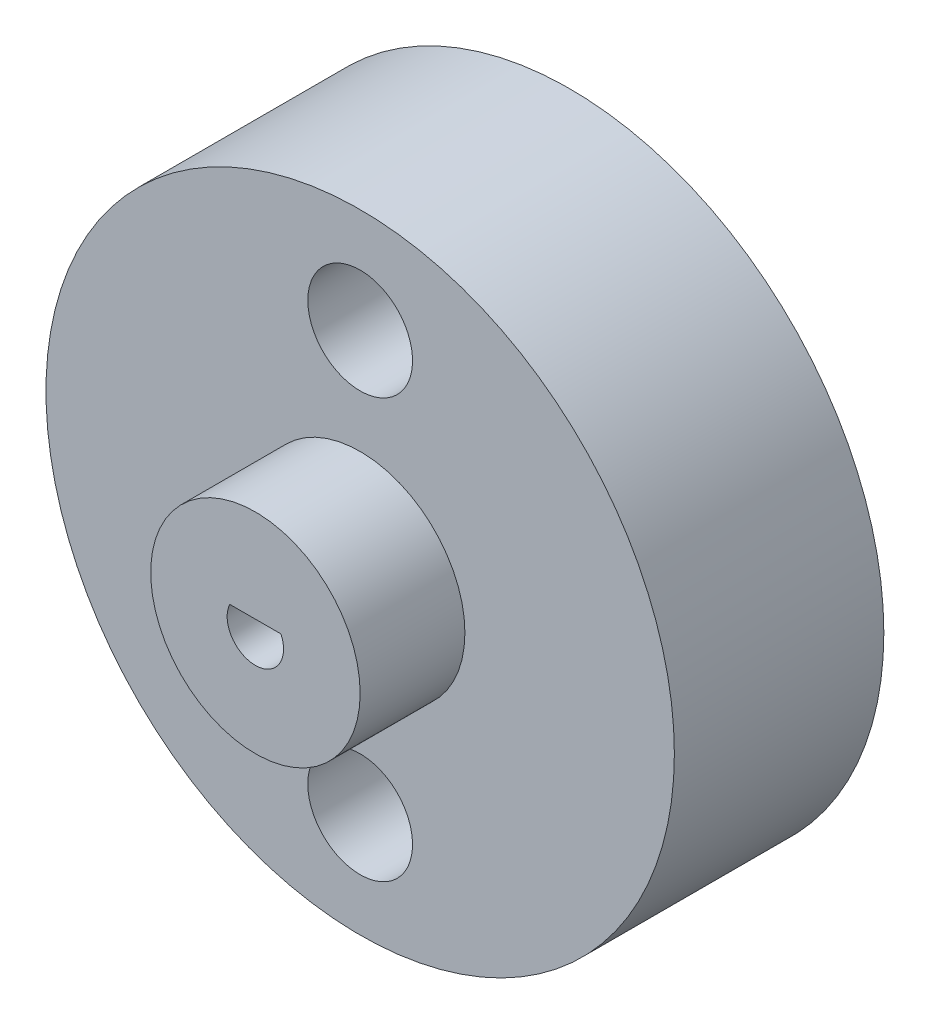
SolidWorks part; units mm, degrees
material "Rubber"
ref_plane "Front Plane" through (0, 0, 0) normal (0, 0, 1) x (1, 0, 0)
ref_plane "Top Plane" through (0, 0, 0) normal (0, 1, 0) x (1, 0, 0)
ref_plane "Right Plane" through (0, 0, 0) normal (1, 0, 0) x (0, 0, -1)
sketch "Sketch1" plane through (0, 0, 0) normal (0, 0, 1) x (1, 0, 0)
  circle A0 centre (0, 0) radius 19.05
  dimension "D1" = 38.1
extrude "Boss-Extrude1" add sketch "Sketch1" along normal blind 12.7
sketch "Sketch2" plane through (0, 0, 12.7) normal (0, 0, 1) x (1, 0, 0)
  circle A0 centre (0, 0) radius 1.7145
  dimension "D1" = 3.429
sketch "Sketch4" plane through (0, 0, 0) normal (0, 0, -1) x (-1, 0, 0)
  line L0 (0, 0) -> (0, -12.7)
  line L1 (0, 0) -> (0, 12.7)
  circle A0 centre (0, 12.7) radius 3.175
  circle A1 centre (0, -12.7) radius 3.175
  dimension "D3" = 6.35
  dimension "D4" = 6.35
  dimension "D1" = 12.7
  dimension "D2" = 12.7
extrude "Cut-Extrude2" cut sketch "Sketch4" against normal through all
sketch "Sketch6" plane through (0, 0, 12.7) normal (0, 0, 1) x (1, 0, 0)
  line L0 (0, 0) -> (0, -1.6962) construction
  line L1 (0, -1.6962) -> (0, 0.7168) construction
  line L2 (0, 0.7168) -> (-1.5574, 0.7168)
  line L3 (-1.5574, 0.7168) -> (1.5463, 0.7168)
  arc A0 (-1.5574, 0.7168) -> (1.5463, 0.7168) centre (-0.0055, -0.0016) ccw
  dimension "D1" = 2.413
extrude "Cut-Extrude4" cut sketch "Sketch6" against normal through all both and the other way through all contours L2 A0 L3
sketch "Sketch7" plane through (0, 0, 12.7) normal (0, 0, 1) x (1, 0, 0)
  circle A1 centre (0, 0) radius 6.35
extrude "Boss-Extrude2" add sketch "Sketch7" along normal blind 6.35
sketch "Sketch8" plane through (0, 0, 0) normal (0, 0, -1) x (-1, 0, 0)
  line L0 (-1.5463, 0.7168) -> (1.5574, 0.7168)
  arc A0 (-1.5463, 0.7168) -> (1.5574, 0.7168) centre (0.0055, -0.0016) ccw
extrude "Cut-Extrude5" cut sketch "Sketch8" against normal through all
